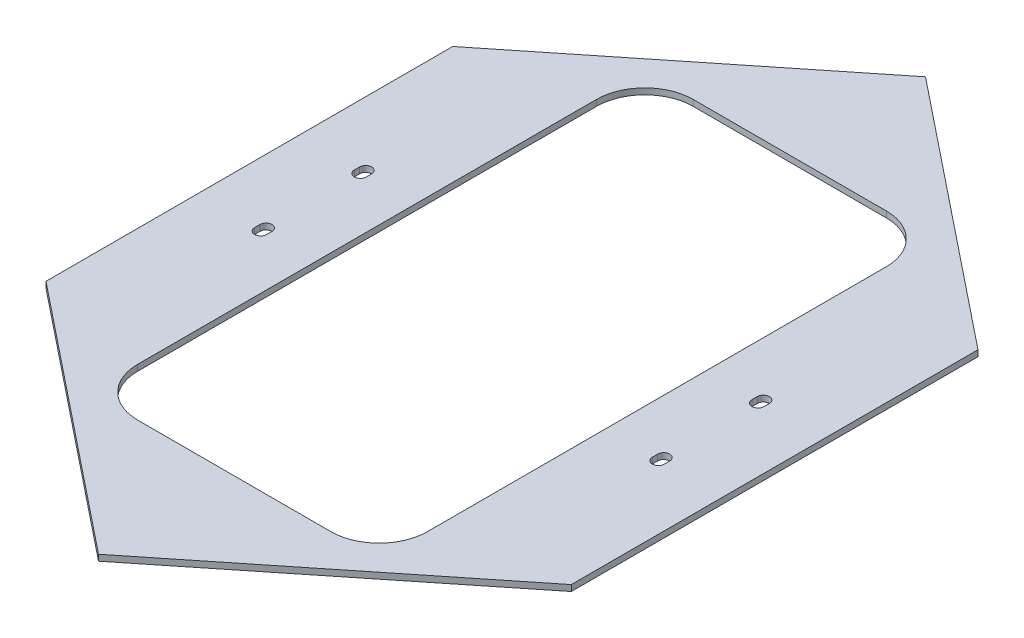
SolidWorks part; units mm, degrees
material "6061-T6 (SS)"
ref_plane "Front Plane" through (0, 0, 0) normal (0, 0, 1) x (1, 0, 0)
ref_plane "Top Plane" through (0, 0, 0) normal (0, 1, 0) x (1, 0, 0)
ref_plane "Right Plane" through (0, 0, 0) normal (1, 0, 0) x (0, 0, -1)
sketch "Sketch1" plane through (0, 0, 0) normal (0, 1, 0) x (1, 0, 0)
  line L0 (0, -434.8618) -> (0, 434.8618) construction
  line L1 (-276.225, 213.8818) -> (0, 434.8618)
  line L2 (276.225, -213.8818) -> (276.225, 213.8818)
  line L3 (0, 434.8618) -> (276.225, 213.8818)
  line L4 (-276.225, -213.8818) -> (-276.225, 213.8818)
  line L5 (276.225, 0) -> (-276.225, 0) construction
  line L6 (-209.1531, -55.1656) -> (-209.1531, 55.1656) construction
  line L7 (101.6, -292.1) -> (-101.6, -292.1)
  line L8 (152.4, -241.3) -> (152.4, 241.3)
  line L9 (101.6, 292.1) -> (-101.6, 292.1)
  line L10 (-152.4, -241.3) -> (-152.4, 241.3)
  line L11 (-228.6, 12.7) -> (228.6, 12.7) construction
  line L12 (-228.6, 12.7) -> (-228.6, -12.7) construction
  line L13 (-228.6, -12.7) -> (228.6, -12.7) construction
  line L14 (228.6, 12.7) -> (228.6, -12.7) construction
  line L15 (-209.1531, 55.1656) -> (-209.1531, 49.6094) construction
  line L16 (-202.8031, 55.1656) -> (-202.8031, 49.6094)
  line L17 (-215.5031, 55.1656) -> (-215.5031, 49.6094)
  line L18 (-209.1531, -55.1656) -> (-209.1531, -49.6094) construction
  line L19 (-202.8031, -55.1656) -> (-202.8031, -49.6094)
  line L20 (-215.5031, -55.1656) -> (-215.5031, -49.6094)
  line L21 (209.1531, -55.1656) -> (209.1531, 55.1656) construction
  line L22 (209.1531, -55.1656) -> (209.1531, -49.6094) construction
  line L23 (202.8031, -55.1656) -> (202.8031, -49.6094)
  line L24 (215.5031, -55.1656) -> (215.5031, -49.6094)
  line L25 (209.1531, 55.1656) -> (209.1531, 49.6094) construction
  line L26 (202.8031, 55.1656) -> (202.8031, 49.6094)
  line L27 (215.5031, 55.1656) -> (215.5031, 49.6094)
  line L28 (276.225, -213.8818) -> (0, -434.8618)
  line L29 (0, -434.8618) -> (-276.225, -213.8818)
  arc A0 (-202.8031, 55.1656) -> (-215.5031, 55.1656) centre (-209.1531, 55.1656) ccw
  arc A1 (-215.5031, 49.6094) -> (-202.8031, 49.6094) centre (-209.1531, 49.6094) ccw
  arc A2 (-202.8031, -55.1656) -> (-215.5031, -55.1656) centre (-209.1531, -55.1656) cw
  arc A3 (-215.5031, -49.6094) -> (-202.8031, -49.6094) centre (-209.1531, -49.6094) cw
  arc A4 (101.6, -292.1) -> (152.4, -241.3) centre (101.6, -241.3) ccw
  arc A5 (-101.6, -292.1) -> (-152.4, -241.3) centre (-101.6, -241.3) cw
  arc A6 (152.4, 241.3) -> (101.6, 292.1) centre (101.6, 241.3) ccw
  arc A7 (-101.6, 292.1) -> (-152.4, 241.3) centre (-101.6, 241.3) ccw
  arc A8 (202.8031, -55.1656) -> (215.5031, -55.1656) centre (209.1531, -55.1656) ccw
  arc A9 (215.5031, -49.6094) -> (202.8031, -49.6094) centre (209.1531, -49.6094) ccw
  arc A10 (202.8031, 55.1656) -> (215.5031, 55.1656) centre (209.1531, 55.1656) cw
  arc A11 (215.5031, 49.6094) -> (202.8031, 49.6094) centre (209.1531, 49.6094) cw
  point P13 (-209.1531, 52.3875)
  point P24 (-209.1531, 0)
  point P31 (-152.4, -292.1)
  point P34 (152.4, 292.1)
  point P37 (-152.4, 292.1)
  point P38 (-209.1531, -52.3875)
  point P46 (209.1531, -52.3875)
  point P51 (209.1531, 0)
  point P53 (209.1531, 52.3875)
  dimension "D10" = 50.8
  dimension "D7" = 6.35
  dimension "D1" = 427.7637
  dimension "D2" = 552.45
  dimension "D3" = 304.8
  dimension "D4" = 584.2
  dimension "D5" = 457.2
  dimension "D6" = 25.4
  dimension "D8" = 110.3312
  dimension "D9" = 209.1531
  dimension "D11" = 5.5562
  dimension "D12" = 869.7237
extrude "Boss-Extrude1" add sketch "Sketch1" along normal mid plane 6.35
equation "\"D9@Sketch1\"=5.234375in+3"
